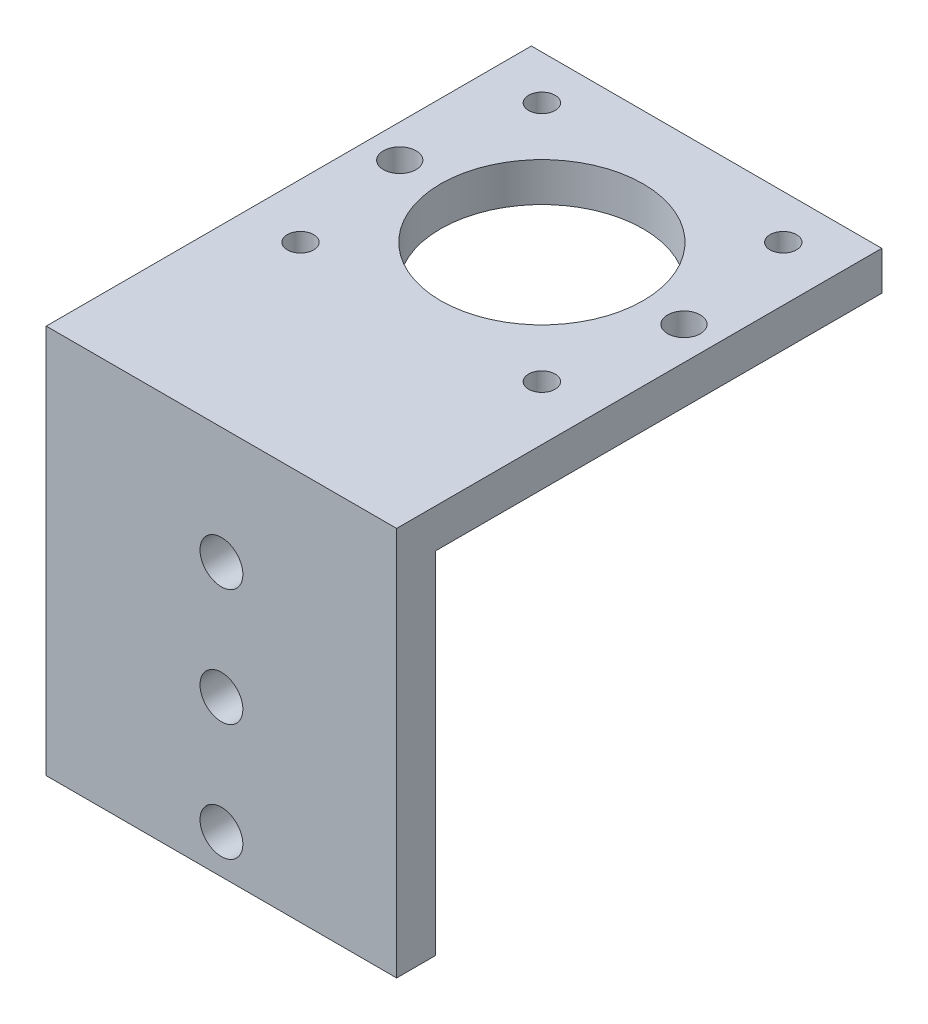
SolidWorks part; units mm, degrees
ref_plane "Front" through (0, 0, 0) normal (0, 0, 1) x (1, 0, 0)
ref_plane "Top" through (0, 0, 0) normal (0, 1, 0) x (1, 0, 0)
ref_plane "Right" through (0, 0, 0) normal (1, 0, 0) x (0, 0, -1)
sketch "Sketch2" plane through (0, 0, 0) normal (0, 1, 0) x (1, 0, 0)
  line L1 (22.5, 21.15) -> (-22.5, 21.15)
  line L2 (22.5, 21.15) -> (22.5, -21.15)
  line L3 (22.5, -21.15) -> (-22.5, -21.15)
  line L4 (-22.5, 21.15) -> (-22.5, -21.15)
  line L5 (0, -21.15) -> (0, 21.15) construction
  line L6 (22.5, 0) -> (-22.5, 0) construction
  point P0 (0, 0)
  dimension "D1" = 42.3
  dimension "D2" = 45
extrude "Boss-Extrude1" add sketch "Sketch2" along normal blind 5
sketch "Sketch3" plane through (22.5, 0, 0) normal (1, 0, 0) x (0, 0, -1)
  line L0 (-21.15, 0) -> (-36.15, 0)
  line L1 (-36.15, 0) -> (-36.15, -45)
  line L2 (-36.15, -45) -> (-41.15, -45)
  line L3 (-41.15, -45) -> (-41.15, 5)
  line L4 (-41.15, 5) -> (-21.15, 5)
  line L5 (-21.15, 5) -> (-21.15, 0)
  point P9 (-43.6968, -37)
  dimension "D1" = 50
  dimension "D2" = 15
  dimension "D3" = 5
extrude "Boss-Extrude2" add sketch "Sketch3" against normal through all
hole_wizard "M5 Clearance Hole1" positions "Sketch4" profile "Sketch5" hole size "M5" standard "ANSI Metric" end condition through all
sketch "Sketch4" plane through (0, 0, 36.15) normal (0, 0, -1) x (-1, 0, 0)
  line L0 (-22.5, 5) -> (22.5, 5) construction
  point P0 (0, -10)
  point P2 (0, -25)
  point P4 (0, -40)
  dimension "D1" = 15
  dimension "D2" = 15
  dimension "D3" = 15
sketch "Sketch5" plane through (0, -10, 36.15) normal (1, 0, 0) x (0, 1, 0)
  line L0 (0, 0) -> (0, 5)
  line L1 (0, 5) -> (2.75, 5)
  line L2 (2.75, 5) -> (2.75, 0)
  line L5 (2.75, 0) -> (0, 0)
  line L11 (0, -6.35) -> (0, 107.95) construction
  dimension "Thru Hole Dia." = 5.5
  dimension "Thru Hole Depth" = 5
sketch "Sketch6" plane through (0, 5, 0) normal (0, 1, 0) x (1, 0, 0)
  line L1 (-15.5, -15.5) -> (15.5, -15.5) construction
  line L2 (-15.5, -15.5) -> (-15.5, 15.5) construction
  line L3 (-15.5, 15.5) -> (15.5, 15.5) construction
  line L4 (15.5, -15.5) -> (15.5, 15.5) construction
  line L5 (0, 15.5) -> (0, -15.5) construction
  line L6 (-15.5, 0) -> (15.5, 0) construction
  circle A0 centre (0, 0) radius 13
  dimension "D3" = 26
  dimension "D1" = 31
  dimension "D2" = 31
extrude "Cut-Extrude1" cut sketch "Sketch6" against normal blind 5
hole_wizard "M3 Clearance Hole1" positions "Sketch7" profile "Sketch8" hole size "M3" standard "ANSI Metric" end condition through all
sketch "Sketch7" plane through (0, 5, 0) normal (0, 1, 0) x (1, 0, 0)
  point P0 (-15.5, 15.5)
  point P3 (-15.5, -15.5)
  point P6 (15.5, -15.5)
  point P9 (15.5, 15.5)
sketch "Sketch8" plane through (-15.5, 5, -15.5) normal (1, 0, 0) x (0, 0, 1)
  line L0 (0, 0) -> (0, 50)
  line L1 (0, 50) -> (1.7, 50)
  line L2 (1.7, 50) -> (1.7, 0)
  line L5 (1.7, 0) -> (0, 0)
  line L11 (0, -6.35) -> (0, 107.95) construction
  dimension "Thru Hole Dia." = 3.4
  dimension "Thru Hole Depth" = 50
hole_wizard "M5x0.8 Tapped Hole1" positions "Sketch9" profile "Sketch10" tap size "M5x0.8" standard "ANSI Metric" end condition through all
sketch "Sketch9" plane through (0, 5, 0) normal (0, 1, 0) x (1, 0, 0)
  line L0 (-18.25, 0) -> (18.25, 0) construction
  point P0 (-18.25, 0)
  point P2 (18.25, 0)
  dimension "D1" = 36.5
sketch "Sketch10" plane through (-18.25, 5, 0) normal (1, 0, 0) x (0, 0, 1)
  line L0 (0, 0) -> (0, 50)
  line L1 (0, 50) -> (2.1, 50)
  line L2 (2.1, 50) -> (2.1, 0)
  line L5 (2.1, 0) -> (0, 0)
  line L11 (0, -6.35) -> (0, 107.95) construction
  dimension "Thru Tap Drill Dia." = 4.2
  dimension "Thru Tap Drill Depth" = 50
cosmetic thread "Hole Thread1" parameters "D2"=5
cosmetic thread "Hole Thread2" parameters "D2"=5
